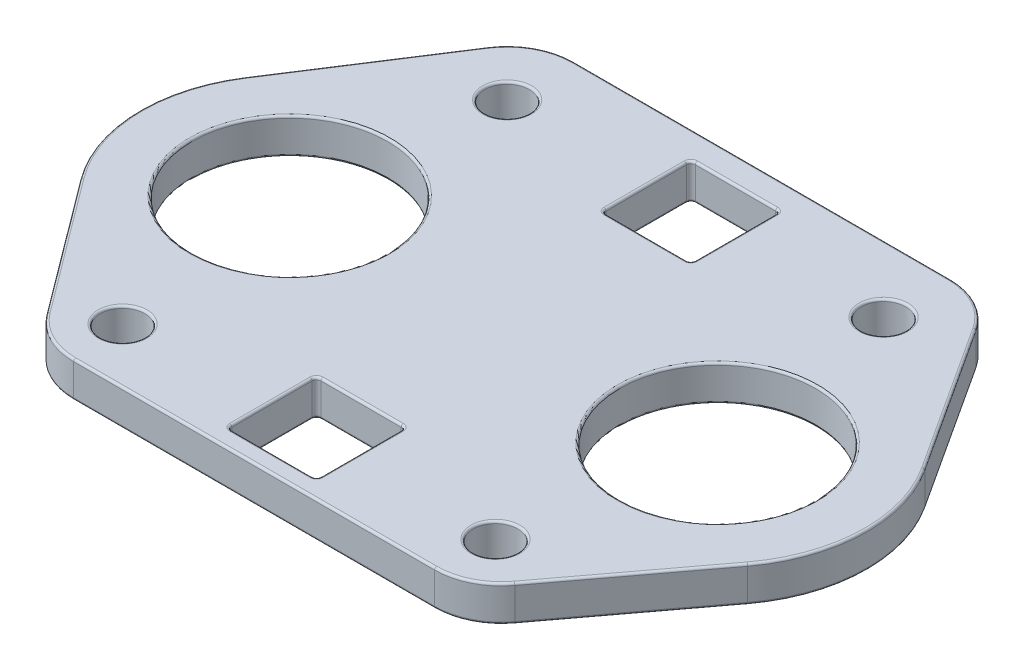
SolidWorks part; units mm, degrees
ref_plane "前视基准面" through (0, 0, 0) normal (0, 0, 1) x (1, 0, 0)
ref_plane "上视基准面" through (0, 0, 0) normal (0, 1, 0) x (1, 0, 0)
ref_plane "右视基准面" through (0, 0, 0) normal (1, 0, 0) x (0, 0, -1)
sketch "草图1" plane through (0, 0, 0) normal (0, 1, 0) x (1, 0, 0)
  line L0 (0, 0) -> (96, 0) construction
  line L3 (5.7733, 58) -> (90.2263, 58)
  line L4 (-6.8228, 51.1447) -> (-28.1315, 18.19)
  line L5 (102.8017, 51.1768) -> (124.1687, 18.316)
  line L6 (7.5209, -56) -> (88.5, -56)
  line L7 (-4.4991, -49.9732) -> (-26.8448, -20.0403)
  line L8 (100.5, -49.9999) -> (122.8799, -20.1598)
  arc A0 (-28.1315, 18.19) -> (-26.8448, -20.0403) centre (0, 0) ccw
  arc A1 (122.8799, -20.1598) -> (124.1687, 18.316) centre (96, 0) ccw
  circle A2 centre (0, 0) radius 22
  circle A3 centre (96, 0) radius 22
  arc A4 (102.8017, 51.1768) -> (90.2263, 58) centre (90.2263, 43) ccw
  arc A5 (5.7733, 58) -> (-6.8228, 51.1447) centre (5.7733, 43) ccw
  arc A6 (100.5, -49.9999) -> (88.5, -56) centre (88.5, -41) cw
  arc A7 (7.5209, -56) -> (-4.4991, -49.9732) centre (7.5209, -41) cw
  point P3 (48, 0)
  dimension "D3" = 44
  dimension "D5" = 15
  dimension "D4" = 15
  dimension "D1" = 96
  dimension "D2" = 56
  dimension "D6" = 58
extrude "凸台-拉伸1" add sketch "草图1" along normal blind 8
sketch "草图2" plane through (0, 0, 0) normal (0, -1, 0) x (1, 0, 0)
  circle A0 centre (5.7733, -43) radius 5
  circle A1 centre (90.2263, -43) radius 5
  dimension "D1" = 10
extrude "切除-拉伸1" cut sketch "草图2" against normal through all
sketch "草图4" plane through (0, 8, 0) normal (0, 1, 0) x (1, 0, 0)
  line L0 (0.7978, -54.4089) -> (7.5209, -41) construction
  line L1 (95.2082, -54.4164) -> (88.5, -41) construction
  arc A0 (-4.4991, -49.9732) -> (7.5209, -56) centre (7.5209, -41) ccw construction
  circle A1 centre (6.1763, -43.6818) radius 5
  arc A2 (88.5, -56) -> (100.5, -49.9999) centre (88.5, -41) ccw construction
  circle A3 centre (89.8416, -43.6833) radius 5
  dimension "D2" = 10
  dimension "D3" = 10
  dimension "D1" = 12
  dimension "D4" = 12
extrude "切除-拉伸2" cut sketch "草图4" against normal through all
sketch "草图5" plane through (0, 8, 0) normal (0, 1, 0) x (1, 0, 0)
  line L0 (0, 0) -> (96, 0) construction
  line L1 (48, 0) -> (48, 42) construction
  line L2 (39, -32) -> (57, -32)
  line L3 (39, 52) -> (57, 52)
  line L4 (38, 51) -> (38, 33)
  line L5 (39, 32) -> (57, 32)
  line L6 (58, 51) -> (58, 33)
  line L7 (38, 52) -> (58, 32) construction
  line L8 (38, 32) -> (58, 52) construction
  line L9 (58, -51) -> (58, -33)
  line L10 (39, -52) -> (57, -52)
  line L11 (38, -51) -> (38, -33)
  arc A0 (38, 33) -> (39, 32) centre (39, 33) ccw
  arc A1 (57, 32) -> (58, 33) centre (57, 33) ccw
  arc A2 (58, 51) -> (57, 52) centre (57, 51) ccw
  arc A3 (39, 52) -> (38, 51) centre (39, 51) ccw
  arc A4 (57, -32) -> (58, -33) centre (57, -33) cw
  arc A5 (58, -51) -> (57, -52) centre (57, -51) cw
  arc A6 (38, -33) -> (39, -32) centre (39, -33) cw
  arc A7 (39, -52) -> (38, -51) centre (39, -51) cw
  dimension "D4" = 1
  dimension "D1" = 42
  dimension "D2" = 20
  dimension "D3" = 20
extrude "切除-拉伸3" cut sketch "草图5" against normal through all
fillet "圆角1" radius 0.5 68 edges at (96, 0, 22) (0, 0, 22) (47.9998, 0, -58) (-1.397, 0, -56.1752) (-17.4772, 0, -34.6674) (-33.4812, 0, 1.1269) (-15.672, 0, 35.0068) (0.7978, 0, 54.4089) (48.0104, 0, 56) (95.2082, 0, 54.4164) (111.69, 0, 35.0799) (129.581, 0, 1.1248) (113.4852, 0, -34.7464) (97.3799, 0, -56.1843) (90.2263, 0, -48) (5.7733, 0, -48) (89.8416, 0, 48.6833) (6.1763, 0, 48.6818) (57.7071, 0, 32.2929) (58, 0, 42) (57.7071, 0, 51.7071) (48, 0, 52) (38.2929, 0, 51.7071) (38, 0, 42) (38.2929, 0, 32.2929) (48, 0, 32) (38.2929, 0, -51.7071) (48, 0, -52) (57.7071, 0, -51.7071) (58, 0, -42) (57.7071, 0, -32.2929) (48, 0, -32) (38.2929, 0, -32.2929) (38, 0, -42) (96, 8, 22) (113.4852, 8, -34.7464) (129.581, 8, 1.1248) (111.69, 8, 35.0799) (95.2082, 8, 54.4164) (48.0104, 8, 56) (0.7978, 8, 54.4089) (-15.672, 8, 35.0068) (-33.4812, 8, 1.1269) (-17.4772, 8, -34.6674) (-1.397, 8, -56.1752) (47.9998, 8, -58) (97.3799, 8, -56.1843) (0, 8, 22) (90.2263, 8, -48) (5.7733, 8, -48) (89.8416, 8, 48.6833) (6.1763, 8, 48.6818) (38, 8, 42) (38.2929, 8, 51.7071) (48, 8, 52) (57.7071, 8, 51.7071) (58, 8, 42) (57.7071, 8, 32.2929) (48, 8, 32) (38.2929, 8, 32.2929) (48, 8, -32) (57.7071, 8, -32.2929) (58, 8, -42) (57.7071, 8, -51.7071) (48, 8, -52) (38.2929, 8, -51.7071) (38, 8, -42) (38.2929, 8, -32.2929)
